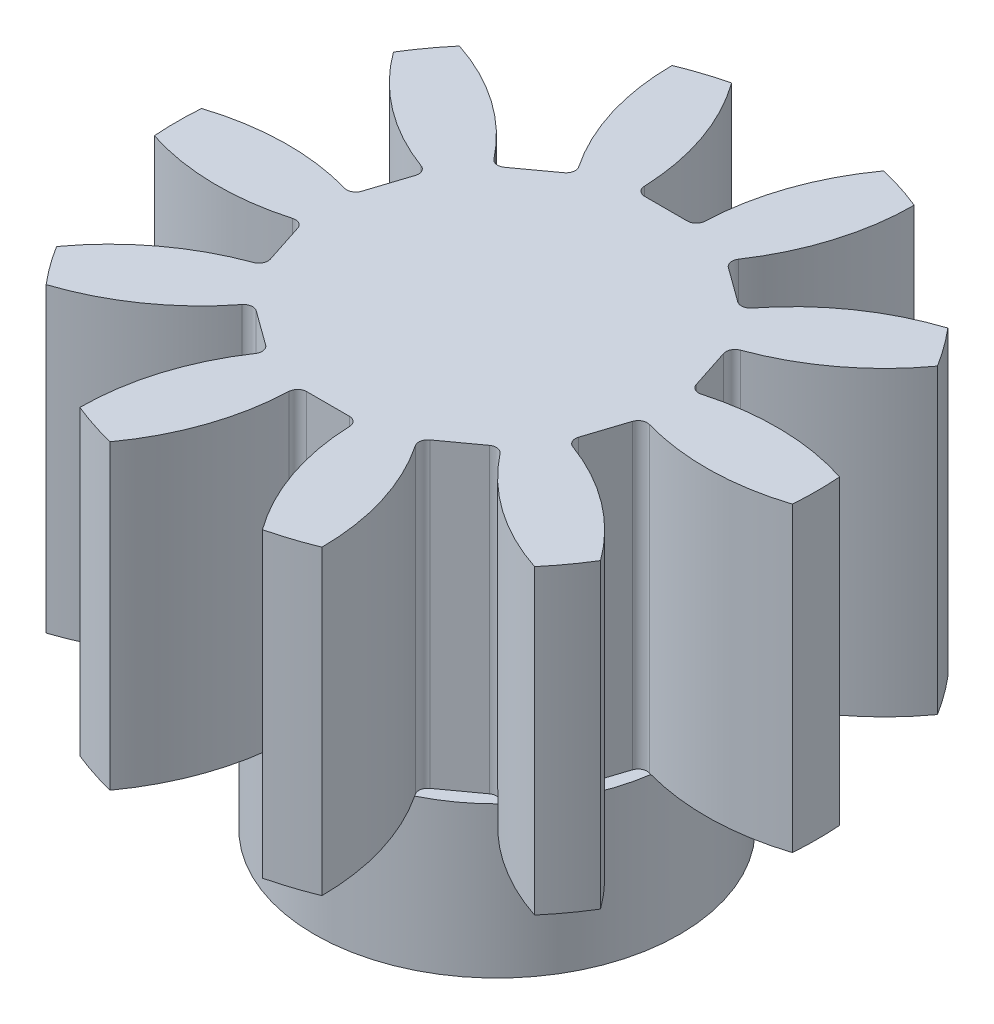
SolidWorks part; units mm, degrees
ref_plane "Front Plane" through (0, 0, 0) normal (0, 0, 1) x (1, 0, 0)
ref_plane "Top Plane" through (0, 0, 0) normal (0, 1, 0) x (1, 0, 0)
ref_plane "Right Plane" through (0, 0, 0) normal (1, 0, 0) x (0, 0, -1)
sketch "Sketch1" plane through (0, 0, 0) normal (0, 1, 0) x (1, 0, 0)
  line L0 (-1.6, 2.5966) -> (1.6, 2.5966)
  circle A0 centre (0, 0) radius 3.05
  circle A1 centre (0, 0) radius 6.05
  dimension "D1" = 6.1
  dimension "D3" = 3
  dimension "D2" = 3.2
extrude "Boss-Extrude1" add sketch "Sketch1" along normal blind 5 contours A1 A0 | L0 A0
sketch "Sketch2" plane through (0, 5, 0) normal (0, 1, 0) x (1, 0, 0)
  circle A0 centre (0, 0) radius 10.6
  dimension "D1" = 21.2
extrude "Boss-Extrude2" add sketch "Sketch2" along normal blind 10
sketch "Sketch3" plane through (0, 15, 0) normal (0, 1, 0) x (1, 0, 0)
  line L0 (0, 0) -> (0, 3.0551) construction
  line L1 (0, 10.6) -> (0, 5.6)
  line L2 (0.7054, 5.6) -> (-0.7054, 5.6)
  line L3 (-9, 13.6) -> (9, 13.6)
  circle A0 centre (0, 0) radius 10.6 construction
  arc A1 (1.0052, 5.8892) -> (9, 13.6) centre (9, 5.6) cw
  arc A2 (-1.0052, 5.8892) -> (-9, 13.6) centre (-9, 5.6) ccw
  arc A3 (0.7054, 5.6) -> (1.0052, 5.8892) centre (0.7054, 5.9) ccw
  arc A4 (-0.7054, 5.6) -> (-1.0052, 5.8892) centre (-0.7054, 5.9) cw
  point P10 (0, 5.6)
  point P17 (1, 5.6)
  point P20 (-1, 5.6)
  circle M7 centre (0, 0) radius 10.6
  dimension "D1" = 8
  dimension "D5" = 0.3
  dimension "D2" = 5
  dimension "D3" = 2
  dimension "D4" = 8
extrude "Cut-Extrude1" cut sketch "Sketch3" against normal up to surface (10 mm away) contours L0 A1 L3 M7 | L0 L3 A2 M7 | A4 L2 L1 A2 M7 | L2 A3 A1 L1 M7 up to face at (0, 5, 6.05)
pattern_circular "CirPattern1" count 10 over 360 about axis through (0, 0, 0) along (0, 1, 0) of "Cut-Extrude1"
